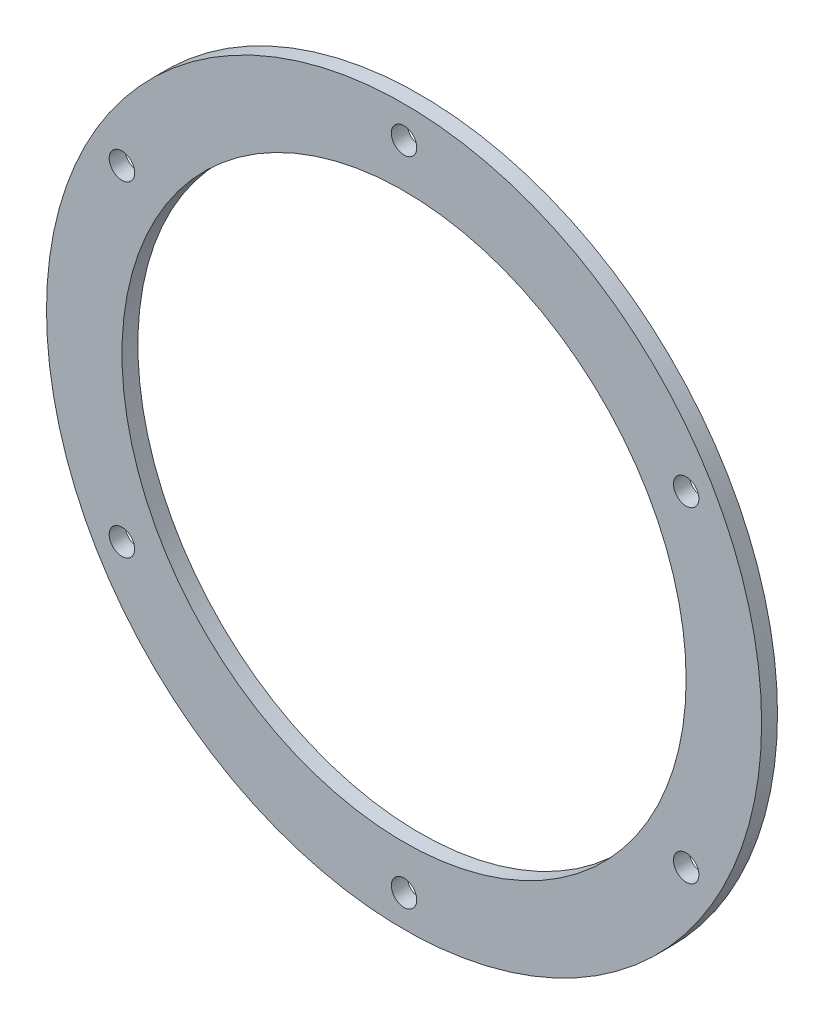
SolidWorks part; units mm, degrees
material "A-玻璃纤维"
ref_plane "前视基准面" through (0, 0, 0) normal (0, 0, 1) x (1, 0, 0)
ref_plane "上视基准面" through (0, 0, 0) normal (0, 1, 0) x (1, 0, 0)
ref_plane "右视基准面" through (0, 0, 0) normal (1, 0, 0) x (0, 0, -1)
sketch "草图1" plane through (0, 0, 0) normal (0, 0, 1) x (1, 0, 0)
  circle A0 centre (0, 0) radius 45
  circle A1 centre (0, 0) radius 35.5
  circle A2 centre (0, 0) radius 41 construction
  circle A3 centre (0, 41) radius 1.6
  circle A4 centre (35.507, 20.5) radius 1.6
  circle A5 centre (35.507, -20.5) radius 1.6
  circle A6 centre (0, -41) radius 1.6
  circle A7 centre (-35.507, -20.5) radius 1.6
  circle A8 centre (-35.507, 20.5) radius 1.6
  point P19 (0, 0)
  dimension "D1" = 71
  dimension "D2" = 90
  dimension "D3" = 82
  dimension "D4" = 3.2
  dimension "D5" = 6
extrude "凸台-拉伸1" add sketch "草图1" along normal blind 2
